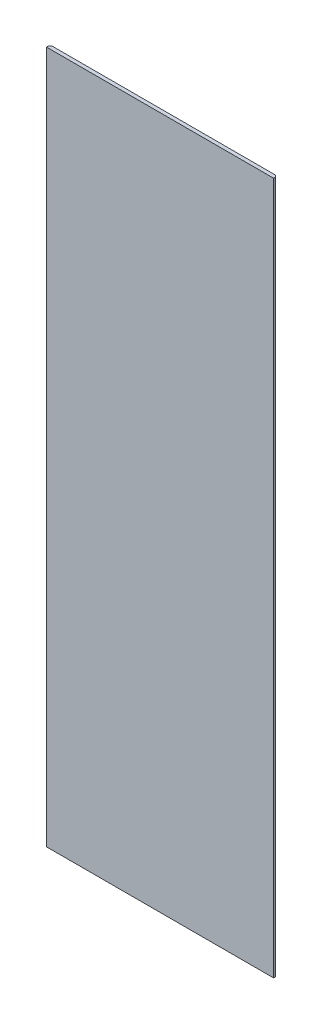
SolidWorks part; units mm, degrees
material "6061-T6 (SS)"
ref_plane "Front Plane" through (0, 0, 0) normal (0, 0, 1) x (1, 0, 0)
ref_plane "Top Plane" through (0, 0, 0) normal (0, 1, 0) x (1, 0, 0)
ref_plane "Right Plane" through (0, 0, 0) normal (1, 0, 0) x (0, 0, -1)
sketch "Sketch1" plane through (0, 0, 0) normal (0, 0, 1) x (1, 0, 0)
  line L1 (49.2063, -150) -> (-49.2062, -150)
  line L2 (49.2063, -150) -> (49.2063, 150)
  line L3 (49.2063, 150) -> (-49.2062, 150)
  line L4 (-49.2062, -150) -> (-49.2062, 150)
  line L5 (49.2063, -150) -> (-49.2062, 150) construction
  line L6 (49.2063, 150) -> (-49.2062, -150) construction
  point P0 (0, 0)
  dimension "D1" = 300
  dimension "D2" = 98.4125
extrude "Boss-Extrude1" add sketch "Sketch1" along normal mid plane 1.5875
chamfer "Chamfer1" distance 0.7937 angle 45 4 edges at (0, -150, -0.7937) (-49.2062, 0, -0.7937) (0, 150, -0.7937) (49.2063, 0, -0.7937)
